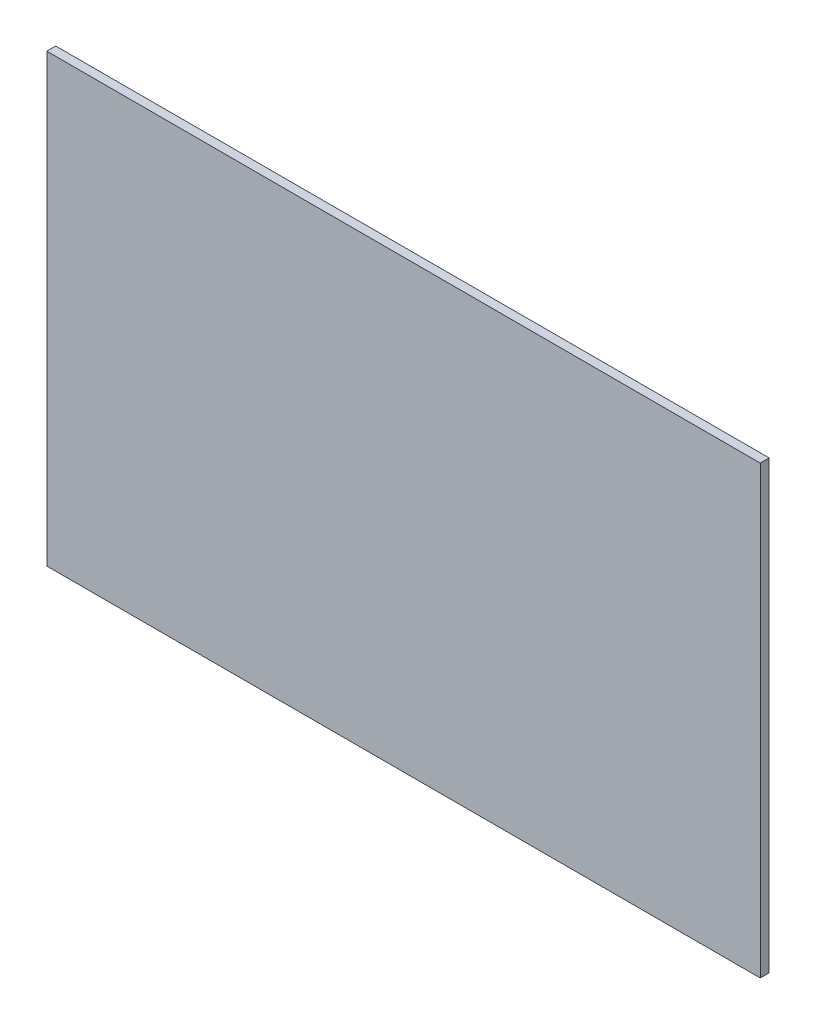
SolidWorks part; units mm, degrees
ref_plane "Plan de face" through (0, 0, 0) normal (0, 0, 1) x (1, 0, 0)
ref_plane "Plan de dessus" through (0, 0, 0) normal (0, 1, 0) x (1, 0, 0)
ref_plane "Plan de droite" through (0, 0, 0) normal (1, 0, 0) x (0, 0, -1)
sketch "Esquisse1" plane through (0, 0, 0) normal (0, 0, 1) x (1, 0, 0)
  line L1 (-80, 50) -> (80, 50)
  line L2 (-80, 50) -> (-80, -50)
  line L3 (-80, -50) -> (80, -50)
  line L4 (80, 50) -> (80, -50)
  dimension "D1" = 100
  dimension "D2" = 160
  dimension "D3" = 50
  dimension "D4" = 80
extrude "Boss.-Extru.1" add sketch "Esquisse1" along normal blind 2
